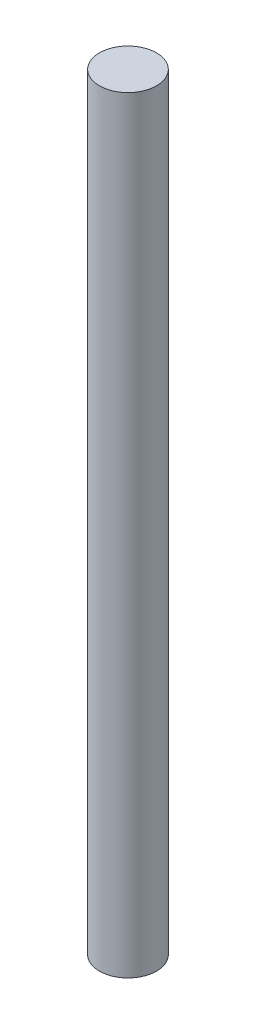
SolidWorks part; units mm, degrees
ref_plane "Front Plane" through (0, 0, 0) normal (0, 0, 1) x (1, 0, 0)
ref_plane "Top Plane" through (0, 0, 0) normal (0, 1, 0) x (1, 0, 0)
ref_plane "Right Plane" through (0, 0, 0) normal (1, 0, 0) x (0, 0, -1)
sketch "Sketch1" plane through (0, 0, 0) normal (0, 1, 0) x (1, 0, 0)
  circle A0 centre (0, 0) radius 1.75
  dimension "1.9" = 3.5
extrude "Boss-Extrude1" add sketch "Sketch1" along normal blind 47
